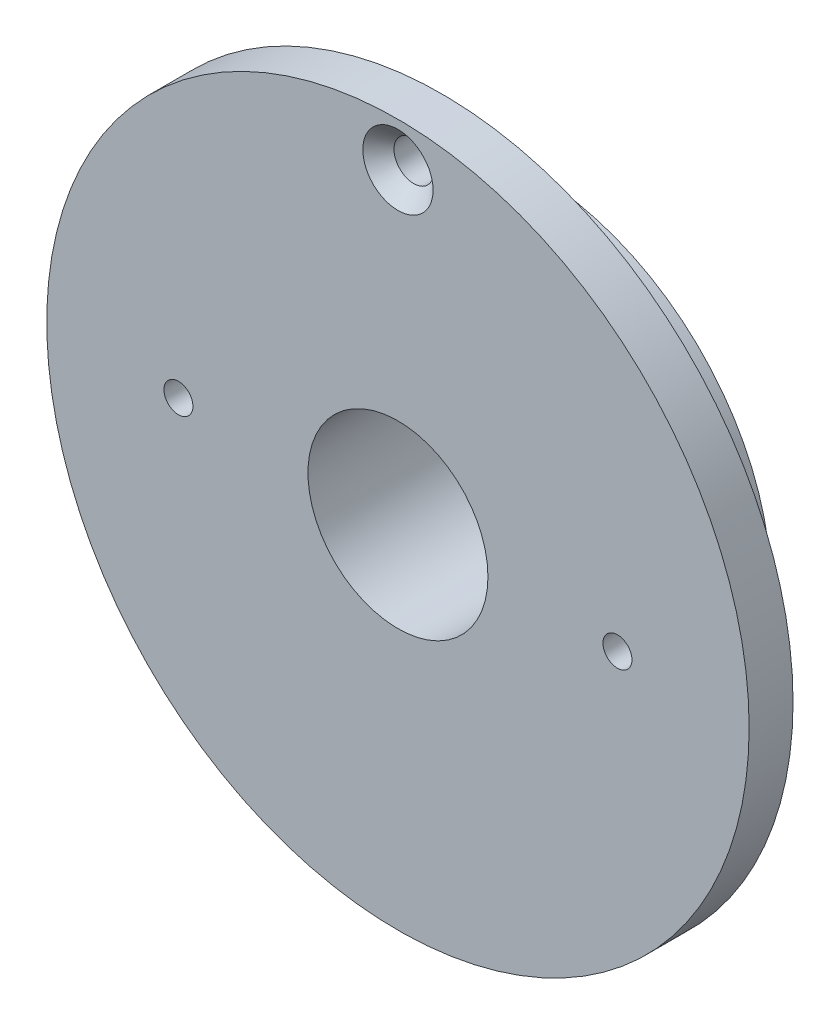
SolidWorks part; units mm, degrees
ref_plane "Alzado" through (0, 0, 0) normal (0, 0, 1) x (1, 0, 0)
ref_plane "Planta" through (0, 0, 0) normal (0, 1, 0) x (1, 0, 0)
ref_plane "Vista lateral" through (0, 0, 0) normal (1, 0, 0) x (0, 0, -1)
sketch "Croquis1" plane through (0, 0, 0) normal (0, 0, 1) x (1, 0, 0)
  circle A0 centre (0, 0) radius 40
  dimension "D1" = 80
extrude "Saliente-Extruir1" add sketch "Croquis1" along normal blind 5
sketch "Croquis2" plane through (0, 0, 0) normal (1, 0, 0) x (0, 0, -1)
  line L0 (-20.6228, 35) -> (12.2012, 35) construction
  line L1 (-5, 35) -> (-5, 39)
  line L2 (-5, 40) -> (-5, -40) construction
  line L3 (-5, 39) -> (-3.2, 37.25)
  line L4 (-3.2, 37.25) -> (0, 37.25)
  line L5 (0, -40) -> (0, 40) construction
  line L6 (0, 37.25) -> (0, 35)
  line L7 (0, 35) -> (-5, 35)
  dimension "D1" = 35
  dimension "D2" = 8
  dimension "D3" = 1.8
  dimension "D4" = 4.5
revolve "Cortar-Revolución1" cut sketch "Croquis2" angle 360 about L0
sketch "Croquis3" plane through (0, 0, 0) normal (0, 0, -1) x (-1, 0, 0)
  circle A0 centre (0, 0) radius 27.5
  dimension "D1" = 55
extrude "Saliente-Extruir2" add sketch "Croquis3" along normal blind 10
hole_wizard "Taladro roscado M41" positions "Croquis5" profile "Croquis4" tap size "M4" standard "DIN" end condition through all
sketch "Croquis5" plane through (0, 0, 5) normal (0, 0, 1) x (1, 0, 0)
  point P0 (-25, 0)
  point P1 (25, 0)
  dimension "D1" = 25
  dimension "D2" = 25
sketch "Croquis4" plane through (-25, 0, 5) normal (1, 0, 0) x (0, -1, 0)
  line L0 (0, 0) -> (0, 15)
  line L1 (0, 15) -> (1.65, 15)
  line L2 (1.65, 15) -> (1.65, 0)
  line L5 (1.65, 0) -> (0, 0)
  line L11 (0, -6.35) -> (0, 107.95) construction
  dimension "Diámetro de perforador para roscar hasta el siguiente" = 3.3
  dimension "Profundidad de perforador para roscar hasta el siguiente" = 15
cosmetic thread "Rosca de taladro1" parameters "D2"=4
cosmetic thread "Rosca de taladro2" parameters "D2"=4
sketch "Croquis6" plane through (0, 0, 5) normal (0, 0, 1) x (1, 0, 0)
  circle A0 centre (0, 0) radius 10.25
  dimension "D1" = 20.5
extrude "Cortar-Extruir1" cut sketch "Croquis6" against normal blind 34.8
